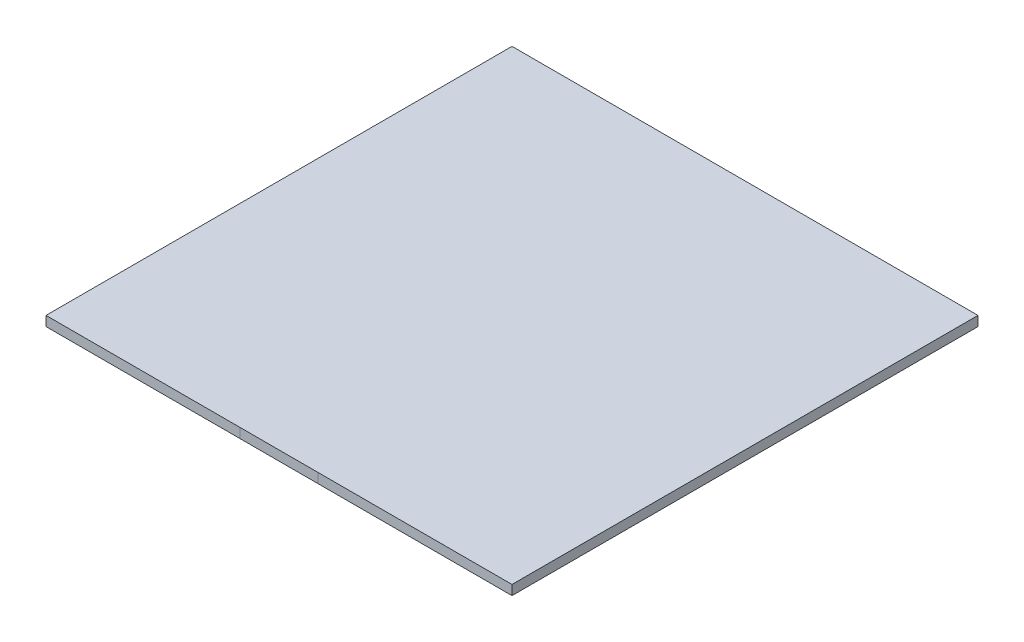
SolidWorks part; units mm, degrees
material "6061 Alloy"
ref_plane "Front Plane" through (0, 0, 0) normal (0, 0, 1) x (1, 0, 0)
ref_plane "Top Plane" through (0, 0, 0) normal (0, 1, 0) x (1, 0, 0)
ref_plane "Right Plane" through (0, 0, 0) normal (1, 0, 0) x (0, 0, -1)
sketch "Sketch2" plane through (0, 0, 0) normal (0, 0, 1) x (1, 0, 0)
  line L1 (0, 0) -> (152.4, 0)
  line L2 (0, 0) -> (0, -3.175)
  line L3 (0, -3.175) -> (152.4, -3.175)
  line L4 (152.4, 0) -> (152.4, -3.175)
  dimension "D1" = 152.4
  dimension "D2" = 3.175
extrude "Boss-Extrude1" add sketch "Sketch2" along normal blind 152.4
sketch "Sketch3" plane through (0, 0, 0) normal (0, 1, 0) x (1, 0, 0)
  line L0 (152.4, -152.4) -> (0, -152.4) construction
  line L1 (76.2, -152.4) -> (76.2, -144.2846) construction
  point P0 (76.2, -152.4)
sketch "Sketch4" plane through (0, 0, 152.4) normal (0, 0, 1) x (1, 0, 0)
  line L0 (152.4, 0) -> (0, 0) construction
  line L1 (63.5, 0) -> (88.9, 0)
  line L2 (63.5, 0) -> (63.5, -3.175)
  line L3 (63.5, -3.175) -> (88.9, -3.175)
  line L4 (88.9, 0) -> (88.9, -3.175)
  line L5 (0, -3.175) -> (152.4, -3.175) construction
  line L6 (0, 0) -> (0, -3.175) construction
  line L7 (152.4, -3.175) -> (152.4, 0) construction
  point P8 (0, -1.5875)
  point P11 (152.4, -1.5875)
  dimension "D1" = 63.5
  dimension "D2" = 63.5
split line "Split Line1"
